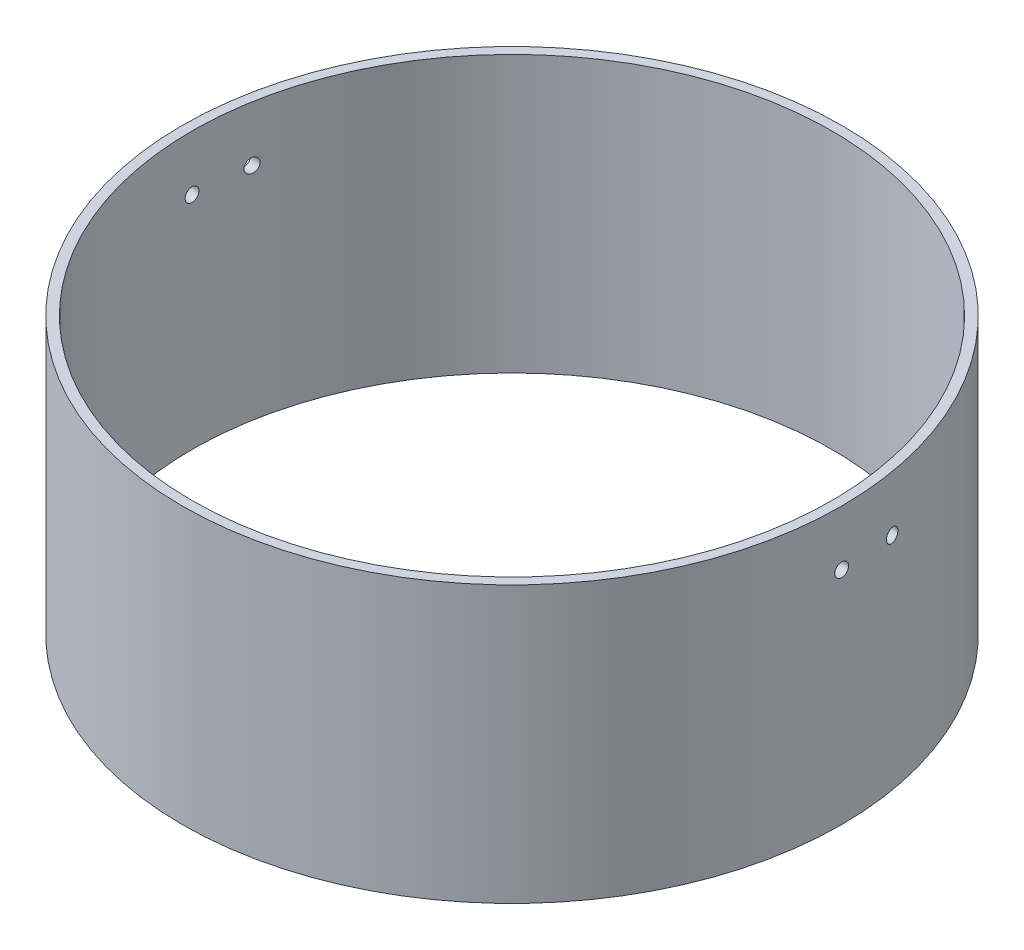
SolidWorks part; units mm, degrees
ref_plane "Front Plane" through (0, 0, 0) normal (0, 0, 1) x (1, 0, 0)
ref_plane "Top Plane" through (0, 0, 0) normal (0, 1, 0) x (1, 0, 0)
ref_plane "Right Plane" through (0, 0, 0) normal (1, 0, 0) x (0, 0, -1)
sketch "Sketch1" plane through (0, 0, 0) normal (0, 1, 0) x (1, 0, 0)
  circle A0 centre (0, 0) radius 75.8825
  dimension "D1" = 151.765
extrude "Boss-Extrude1" add sketch "Sketch1" along normal blind 63.5
sketch "Sketch2" plane through (0, 63.5, 0) normal (0, 1, 0) x (1, 0, 0)
  circle A0 centre (0, 0) radius 73.66
  dimension "D1" = 147.32
extrude "Cut-Extrude1" cut sketch "Sketch2" against normal blind 101.6
sketch "Sketch4" plane through (0, 0, 0) normal (1, 0, 0) x (0, 0, -1)
  line L0 (73.66, 63.5) -> (-73.66, 63.5) construction
  line L1 (75.8825, 63.5) -> (-75.8825, 63.5) construction
  circle A0 centre (0, 50.8) radius 1.5875
  circle A1 centre (12.7, 50.8) radius 1.5875
  dimension "D1" = 3.175
  dimension "D2" = 3.175
  dimension "D5" = 12.7
  dimension "D3" = 12.7
  dimension "D4" = 12.7
extrude "Cut-Extrude4" cut sketch "Sketch4" against normal through all both and the other way through all
